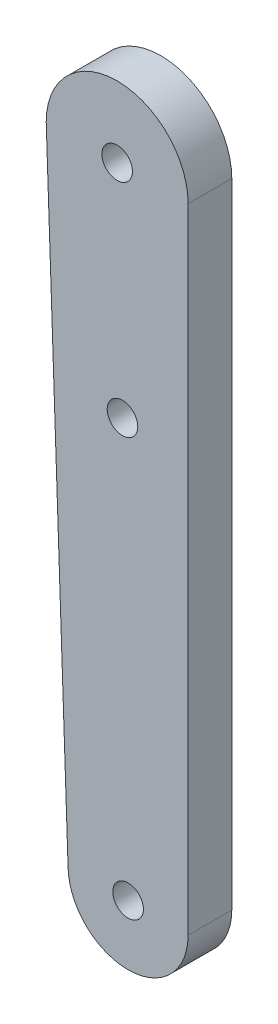
SolidWorks part; units mm, degrees
ref_plane "Front Plane" through (0, 0, 0) normal (0, 0, 1) x (1, 0, 0)
ref_plane "Top Plane" through (0, 0, 0) normal (0, 1, 0) x (1, 0, 0)
ref_plane "Right Plane" through (0, 0, 0) normal (1, 0, 0) x (0, 0, -1)
sketch "Sketch1" plane through (0, 0, 0) normal (0, 0, 1) x (1, 0, 0)
  line L6 (-0.0007, 6.9933) -> (-0.0007, 65.0161)
  line L7 (-13.0007, 65.0161) -> (-11.0007, 6.9933)
  arc A0 (-0.0007, 65.0161) -> (-13.0007, 65.0161) centre (-6.5007, 65.0161) ccw
  arc A1 (-11.0007, 6.9933) -> (-0.0007, 6.9933) centre (-5.5007, 6.9933) ccw
  circle A2 centre (-6.5007, 65.0161) radius 1.4
  circle A3 centre (-5.5007, 6.9933) radius 1.4
  circle A4 centre (-6.0128, 45.0161) radius 1.4
  point P8 (-5.0007, 1.5161)
  point P11 (-6.5007, 71.5161)
  dimension "D1" = 13
  dimension "D4" = 11
  dimension "D5" = 20
  dimension "D2" = 2.8
  dimension "D3" = 2.8
  dimension "D6" = 2.8
  dimension "D7" = 70
extrude "Boss-Extrude2" add sketch "Sketch1" along normal blind 4
